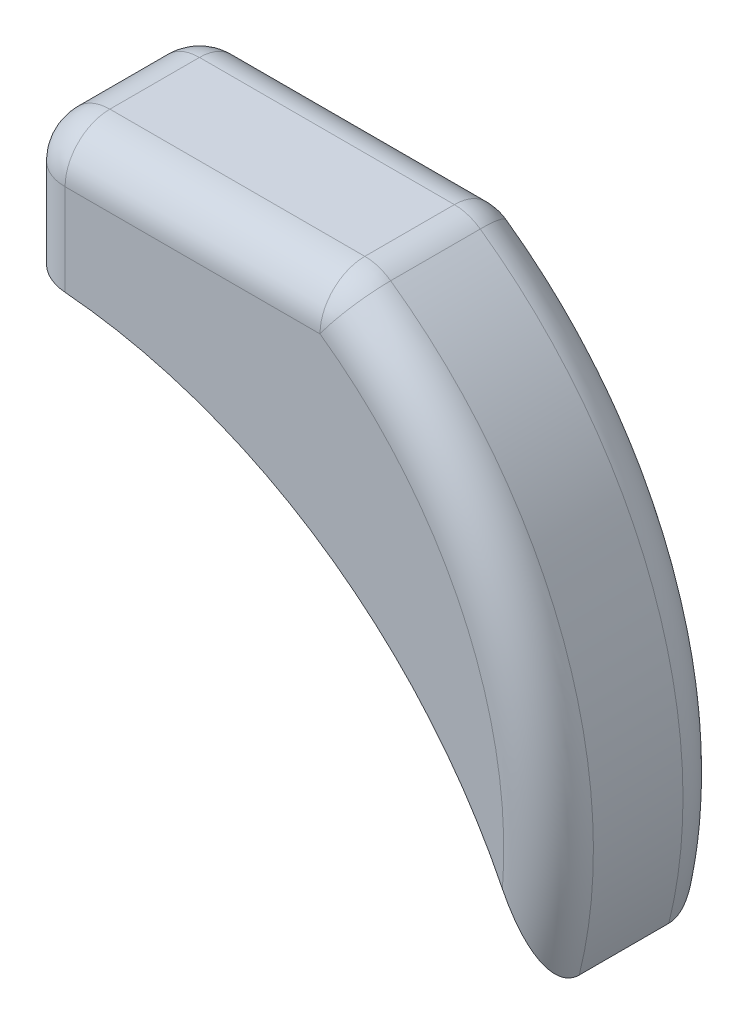
SolidWorks part; units mm, degrees
ref_plane "Plan de face" through (0, 0, 0) normal (0, 0, 1) x (1, 0, 0)
ref_plane "Plan de dessus" through (0, 0, 0) normal (0, 1, 0) x (1, 0, 0)
ref_plane "Plan de droite" through (0, 0, 0) normal (1, 0, 0) x (0, 0, -1)
sketch "Esquisse1" plane through (0, 0, 0) normal (0, 0, 1) x (1, 0, 0)
  line L0 (-47.6925, 0) -> (47.6925, 0) construction
  line L1 (-35, 15) -> (35, 15)
  line L2 (-35, 15) -> (-35, -15)
  line L3 (-35, -15) -> (35, -15)
  line L4 (35, 15) -> (35, -15)
  line L5 (0, 50.3454) -> (0, -36.0614) construction
  line L6 (-35, -15) -> (-35, -275.1686)
  line L7 (-35, -135) -> (85, -135) construction
  circle A0 centre (-35, -135) radius 120
  arc A1 (35, 15) -> (79.7824, -100) centre (-24.0656, -74.2203) cw
  dimension "D1" = 240
  dimension "D4" = 35
  dimension "D5" = 107
  dimension "D2" = 30
  dimension "D3" = 70
extrude "Boss.-Extru.1" add sketch "Esquisse1" along normal mid plane 40 contours A1 L4 L3 A0 | L4 L1 L2 L3
sketch "Esquisse2" plane through (-35, 0, 0) normal (-1, 0, 0) x (0, 0, 1)
  line L0 (0, 15) -> (0, -15) construction
  line L2 (20, -15) -> (-20, -15) construction
  line L3 (20, 0) -> (-20, 0) construction
  line L6 (20, 15) -> (-20, 15) construction
  line L7 (20, 15) -> (20, -15) construction
  circle A0 centre (0, 0) radius 13.505
  dimension "D1" = 27.01
sketch "Esquisse6" plane through (-35, 0, 0) normal (-1, 0, 0) x (0, 0, 1)
  line L0 (20, 15) -> (-20, 15) construction
  line L1 (-20, 15) -> (20, 15)
  line L2 (-20, 15) -> (-20, -25)
  line L3 (-20, -25) -> (20, -25)
  line L4 (20, 15) -> (20, -25)
  line L6 (20, 15) -> (20, -15) construction
  line L7 (-20, 15) -> (-20, -15) construction
  line L8 (20, -15) -> (-20, -15) construction
  dimension "D1" = 10
sketch "Esquisse7" [suppressed] plane through (-30, 0, 0) normal (-1, 0, 0) x (0, 0, 1)
  line L0 (-50.7126, 0) -> (32.9762, 0) construction
  line L1 (0, 30.6791) -> (0, -28.4968) construction
  circle A0 centre (-15, 15) radius 1.5
  circle A1 centre (-15, -15) radius 1.5
  circle A2 centre (15, -15) radius 1.5
  circle A3 centre (15, 15) radius 1.5
  dimension "D1" = 3
  dimension "D2" = 30
  dimension "D3" = 30
fillet "Congé7" radius 10 8 edges at (75.6413, -35.3932, 20) (35, 15, 0) (0, 15, -20) (0, 15, 20) (-35, 15, 0) (-35, 0, -20) (-35, 0, 20) (75.6413, -35.3932, -20)
ref_plane "Plan1" through (0, -54.4196, 0) normal (0, 1, 0) x (1, 0, 0)
ref_plane "Plan2" through (0, -18.6872, 0) normal (0, 1, 0) x (1, 0, 0)
sketch "Esquisse11" plane through (0, -54.4196, 0) normal (0, 1, 0) x (1, 0, 0)
  circle A0 centre (47.5507, 0) radius 1.25
  dimension "D1" = 2.5
sketch "Esquisse12" plane through (0, -18.6872, 0) normal (0, 1, 0) x (1, 0, 0)
  circle A0 centre (-21.6008, 0) radius 1.25
  dimension "D1" = 2.5
extrude "Enlèv. mat.-Extru.5" cut sketch "Esquisse12" along normal blind 15 contours A0
extrude "Enlèv. mat.-Extru.6" cut sketch "Esquisse11" along normal blind 20 contours A0
